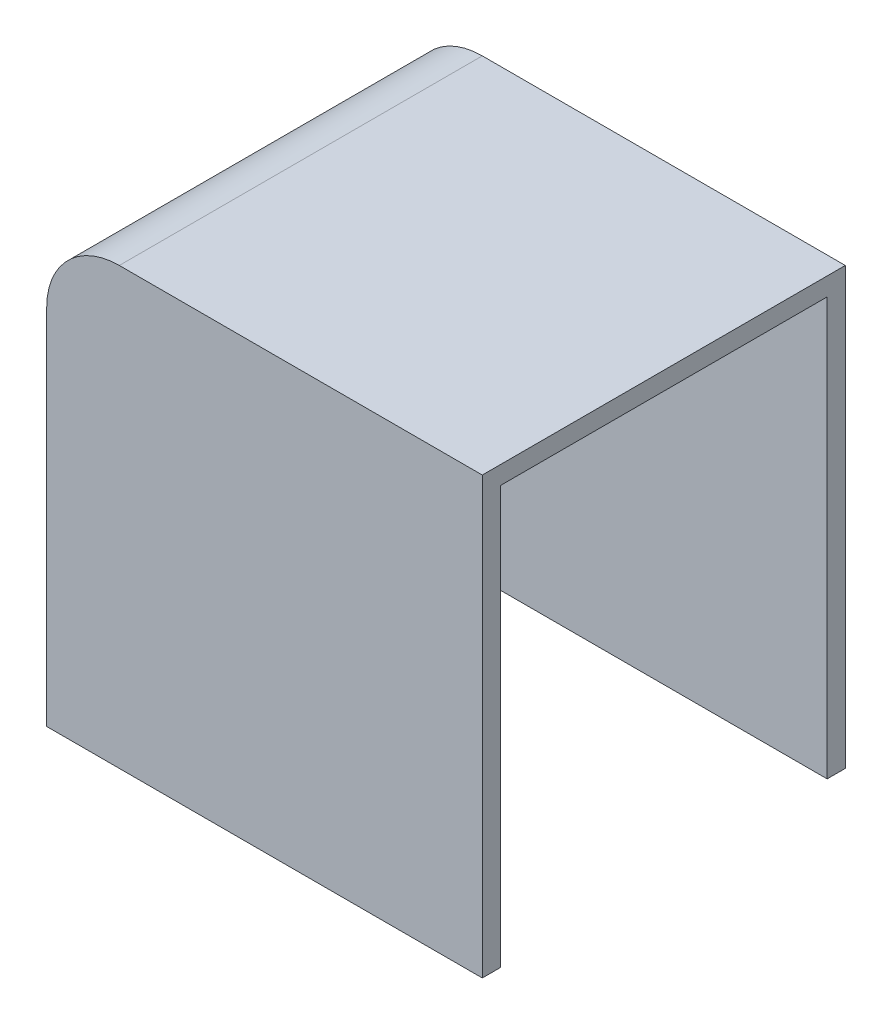
SolidWorks part; units mm, degrees
ref_plane "Plan de face" through (0, 0, 0) normal (0, 0, 1) x (1, 0, 0)
ref_plane "Plan de dessus" through (0, 0, 0) normal (0, 1, 0) x (1, 0, 0)
ref_plane "Plan de droite" through (0, 0, 0) normal (1, 0, 0) x (0, 0, -1)
sketch "Esquisse1" plane through (0, 0, 0) normal (0, 0, 1) x (1, 0, 0)
  line L0 (-12, 0) -> (-12, 10)
  line L1 (-10, 12) -> (0, 12)
  line L2 (0, 12) -> (0, 11.5)
  line L3 (0, 11.5) -> (-9.5, 11.5)
  line L4 (-11.5, 9.5) -> (-11.5, 0)
  line L5 (-11.5, 0) -> (-12, 0)
  arc A0 (-12, 10) -> (-10, 12) centre (-10, 10) cw
  arc A1 (-11.5, 9.5) -> (-9.5, 11.5) centre (-9.5, 9.5) cw
  point P10 (0, 0)
  dimension "D1" = 2
  dimension "D2" = 2
  dimension "D3" = 10
  dimension "D4" = 10
  dimension "D5" = 0.5
  dimension "D6" = 0.5
extrude "Boss.-Extru.1" add sketch "Esquisse1" along normal blind 9
sketch "Esquisse2" plane through (0, 0, 9) normal (0, 0, 1) x (1, 0, 0)
  line L0 (0, 12) -> (0, 0)
  line L1 (0, 0) -> (-12, 0)
  line L6 (-12, 0) -> (-11.5, 0)
  line L7 (-11.5, 0) -> (-11.5, 9.5)
  line L8 (-9.5, 11.5) -> (0, 11.5)
  line L9 (0, 11.5) -> (0, 12)
  line L10 (0, 12) -> (-10, 12)
  line L11 (-12, 10) -> (-12, 0)
  line L16 (0, 12) -> (-10, 12)
  line L17 (-12, 10) -> (-12, 0)
  arc A2 (-9.5, 11.5) -> (-11.5, 9.5) centre (-9.5, 9.5) ccw
  arc A3 (-10, 12) -> (-12, 10) centre (-10, 10) ccw
  arc A5 (-10, 12) -> (-12, 10) centre (-10, 10) ccw
  dimension "D1" = 0
extrude "Boss.-Extru.2" add sketch "Esquisse2" along normal blind 0.5
sketch "Esquisse3" plane through (0, 0, 0) normal (0, 0, -1) x (-1, 0, 0)
  line L0 (0, 12) -> (10, 12) construction
  line L1 (12, 10) -> (12, 0) construction
  line L2 (0, 12) -> (10, 12)
  line L3 (12, 10) -> (12, 0)
  line L4 (0, 12) -> (0, 0)
  line L5 (0, 0) -> (12, 0)
  arc A0 (12, 10) -> (10, 12) centre (10, 10) ccw construction
  arc A1 (12, 10) -> (10, 12) centre (10, 10) ccw
extrude "Boss.-Extru.3" add sketch "Esquisse3" along normal blind 0.5
